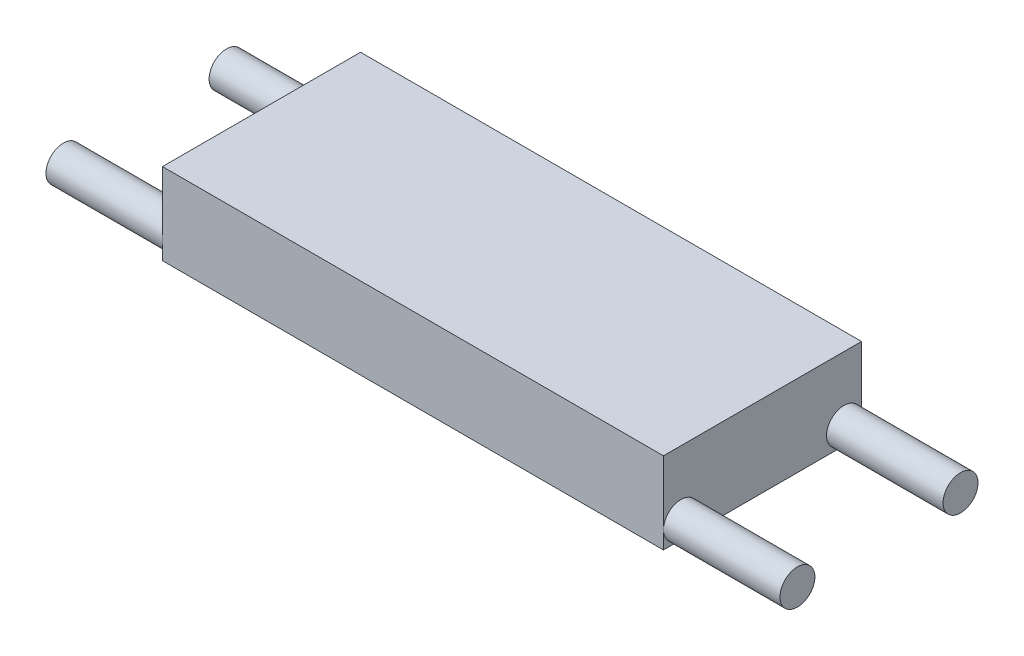
SolidWorks part; units mm, degrees
ref_plane "Front Plane" through (0, 0, 0) normal (0, 0, 1) x (1, 0, 0)
ref_plane "Top Plane" through (0, 0, 0) normal (0, 1, 0) x (1, 0, 0)
ref_plane "Right Plane" through (0, 0, 0) normal (1, 0, 0) x (0, 0, -1)
sketch "Sketch1" plane through (0, 0, 0) normal (0, 1, 0) x (1, 0, 0)
  line L1 (0, 0) -> (43, 0)
  line L2 (0, 0) -> (0, 17)
  line L3 (0, 17) -> (43, 17)
  line L4 (43, 0) -> (43, 17)
  dimension "D1" = 17
  dimension "D2" = 43
extrude "Boss-Extrude1" add sketch "Sketch1" along normal blind 7
sketch "Sketch2" plane through (43, 0, 0) normal (1, 0, 0) x (0, 0, -1)
  line L0 (0, 0) -> (17, 0) construction
  line L1 (17, 7) -> (17, 0) construction
  line L2 (0, 7) -> (0, 0) construction
  circle A0 centre (15.5, 1.5) radius 1.5
  circle A1 centre (1.5, 1.5) radius 1.5
  dimension "D1" = 3
  dimension "D2" = 3
extrude "Boss-Extrude2" add sketch "Sketch2" along normal blind 10
ref_plane "Plane1" through (21.5, 0, 0) normal (1, 0, 0) x (0, 0, -1)
mirror "Mirror1" about plane through (21.5, 0, 0) normal (1, 0, 0) of "Boss-Extrude2"
